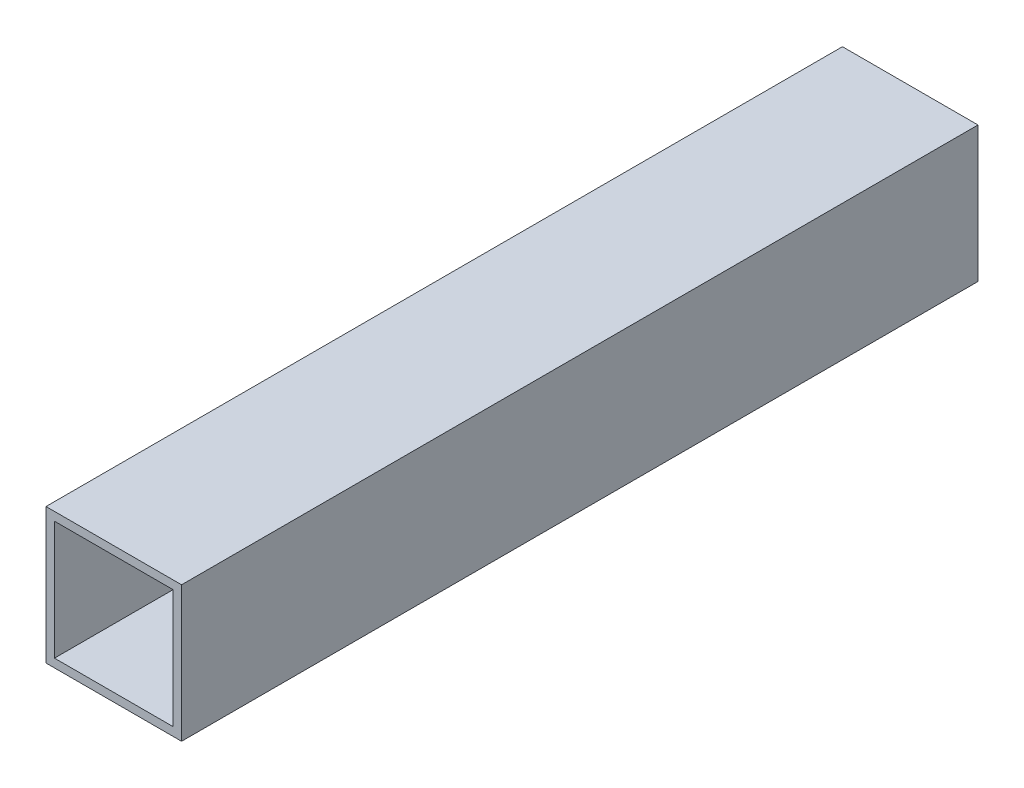
SolidWorks part; units mm, degrees
material "6061-T6 (SS)"
ref_plane "Front Plane" through (0, 0, 0) normal (0, 0, 1) x (1, 0, 0)
ref_plane "Top Plane" through (0, 0, 0) normal (0, 1, 0) x (1, 0, 0)
ref_plane "Right Plane" through (0, 0, 0) normal (1, 0, 0) x (0, 0, -1)
sketch "Sketch1" plane through (0, 0, 0) normal (0, 0, 1) x (1, 0, 0)
  line L0 (-11.1125, 11.1125) -> (11.1125, 11.1125)
  line L2 (-12.7, 12.7) -> (12.7, 12.7)
  line L3 (-12.7, 12.7) -> (-12.7, -12.7)
  line L4 (-12.7, -12.7) -> (12.7, -12.7)
  line L5 (12.7, 12.7) -> (12.7, -12.7)
  line L10 (11.1125, 11.1125) -> (11.1125, -11.1125)
  line L11 (-11.1125, -11.1125) -> (11.1125, -11.1125)
  line L12 (-11.1125, 11.1125) -> (-11.1125, -11.1125)
  point P12 (0, 12.7)
  point P14 (12.7, 0)
  dimension "Wall Thickness" = 1.5875
  dimension "Outside Width" = 25.4
  dimension "Outside Height" = 25.4
  dimension "Inside Height" = 22.225
  dimension "Inside Width" = 22.225
sketch "Sketch2" plane through (0, 0, 0) normal (1, 0, 0) x (0, 0, -1)
  line L0 (76.2, 0) -> (-76.2, 0)
  point P4 (0, 0)
  point P7 (-76.2, 0)
  point P10 (76.2, 0)
  dimension "Length" = 152.4
sketch "Sketch3" plane through (0, 0, 0) normal (0, 0, 1) x (1, 0, 0)
  line L21 (12.7, 12.7) -> (-12.7, 12.7)
  line L22 (12.7, -12.7) -> (12.7, 12.7)
  line L23 (-12.7, -12.7) -> (12.7, -12.7)
  line L24 (-12.7, 12.7) -> (-12.7, -12.7)
  line L25 (12.7, 12.7) -> (-12.7, 12.7)
  line L26 (12.7, -12.7) -> (12.7, 12.7)
  line L27 (-12.7, -12.7) -> (12.7, -12.7)
  line L28 (-12.7, 12.7) -> (-12.7, -12.7)
  line L29 (11.1125, 11.1125) -> (-11.1125, 11.1125)
  line L30 (11.1125, -11.1125) -> (11.1125, 11.1125)
  line L31 (-11.1125, -11.1125) -> (11.1125, -11.1125)
  line L32 (-11.1125, 11.1125) -> (-11.1125, -11.1125)
  line L33 (11.1125, 11.1125) -> (-11.1125, 11.1125)
  line L34 (11.1125, -11.1125) -> (11.1125, 11.1125)
  line L35 (-11.1125, -11.1125) -> (11.1125, -11.1125)
  line L36 (-11.1125, 11.1125) -> (-11.1125, -11.1125)
  dimension "D1" = 0
  dimension "D2" = 0
extrude "Boss-Extrude1" add sketch "Sketch3" along normal up to vertex (76.2 mm away) and the other way up to vertex (76.2 mm away) up to point (0, 0, 76.2) other way up to point (0, 0, -76.2)
sketch "Drawing Reference" plane through (0, 0, 0) normal (1, 0, 0) x (0, 0, -1)
  line L0 (-76.2, 0) -> (76.2, 0) construction
  line L1 (0, -12.7) -> (0, 12.7) construction
  line L2 (-76.2, -12.7) -> (76.2, -12.7) construction
  line L5 (-76.2, 12.7) -> (76.2, 12.7) construction
  point P7 (-57.912, 0)
  point P8 (57.912, 0)
  dimension "D1" = 18.288
sketch "Sketch4" plane through (0, 0, -76.2) normal (0, 0, -1) x (-1, 0, 0)
  line L0 (11.1125, -11.1125) -> (-11.1125, -11.1125) construction
  line L1 (-11.1125, -11.1125) -> (-11.1125, 11.1125) construction
  line L2 (-11.1125, 11.1125) -> (11.1125, 11.1125) construction
  line L3 (11.1125, 11.1125) -> (11.1125, -11.1125) construction
  line L4 (12.7, -12.7) -> (12.7, 12.7)
  line L5 (12.7, 12.7) -> (-12.7, 12.7)
  line L6 (-12.7, 12.7) -> (-12.7, -12.7)
  line L7 (-12.7, -12.7) -> (12.7, -12.7)
  line L8 (12.7, -12.7) -> (12.7, 12.7)
  line L9 (12.7, 12.7) -> (-12.7, 12.7)
  line L10 (-12.7, 12.7) -> (-12.7, -12.7)
  line L11 (-12.7, -12.7) -> (12.7, -12.7)
  line L12 (11.1125, -11.1125) -> (-11.1125, -11.1125)
  line L13 (-11.1125, -11.1125) -> (-11.1125, 11.1125)
  line L14 (-11.1125, 11.1125) -> (11.1125, 11.1125)
  line L15 (11.1125, 11.1125) -> (11.1125, -11.1125)
  dimension "D1" = 0
extrude "Cut-Extrude1" cut sketch "Sketch4" against normal offset from surface (3.175 mm away) 149.225 up to face at (0, 0, 76.2)
equation "\"D1@Drawing Reference\"=\"Outside Width@Sketch1\" * 0.72"
